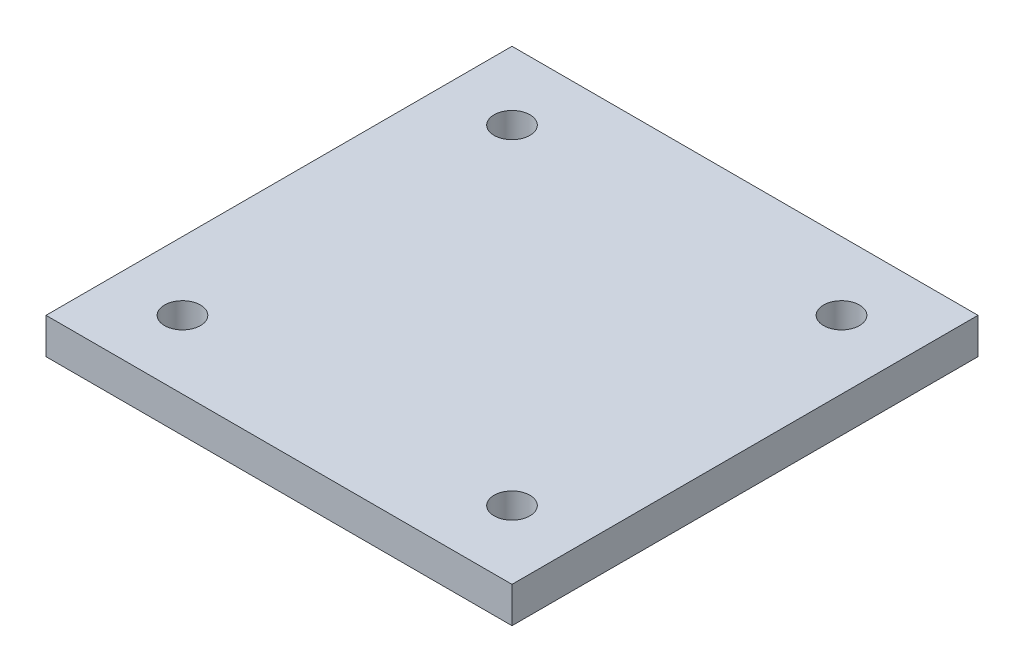
SolidWorks part; units mm, degrees
ref_plane "Front Plane" through (0, 0, 0) normal (0, 0, 1) x (1, 0, 0)
ref_plane "Top Plane" through (0, 0, 0) normal (0, 1, 0) x (1, 0, 0)
ref_plane "Right Plane" through (0, 0, 0) normal (1, 0, 0) x (0, 0, -1)
sketch "Sketch1" plane through (0, 0, 0) normal (0, 1, 0) x (1, 0, 0)
  line L1 (-32.5, -32.5) -> (32.5, -32.5)
  line L2 (-32.5, -32.5) -> (-32.5, 32.5)
  line L3 (-32.5, 32.5) -> (32.5, 32.5)
  line L4 (32.5, -32.5) -> (32.5, 32.5)
  line L5 (-32.5, -32.5) -> (32.5, 32.5) construction
  line L6 (-32.5, 32.5) -> (32.5, -32.5) construction
  circle A0 centre (22.981, -22.981) radius 2.5
  circle A1 centre (-22.981, -22.981) radius 2.5
  circle A2 centre (-22.981, 22.981) radius 2.5
  circle A3 centre (22.981, 22.981) radius 2.5
  point P0 (0, 0)
  point P17 (0, 0)
  dimension "D3" = 5
  dimension "D1" = 65
  dimension "D2" = 65
  dimension "D4" = 32.5
  dimension "D5" = 4
extrude "Boss-Extrude1" add sketch "Sketch1" along normal blind 5
